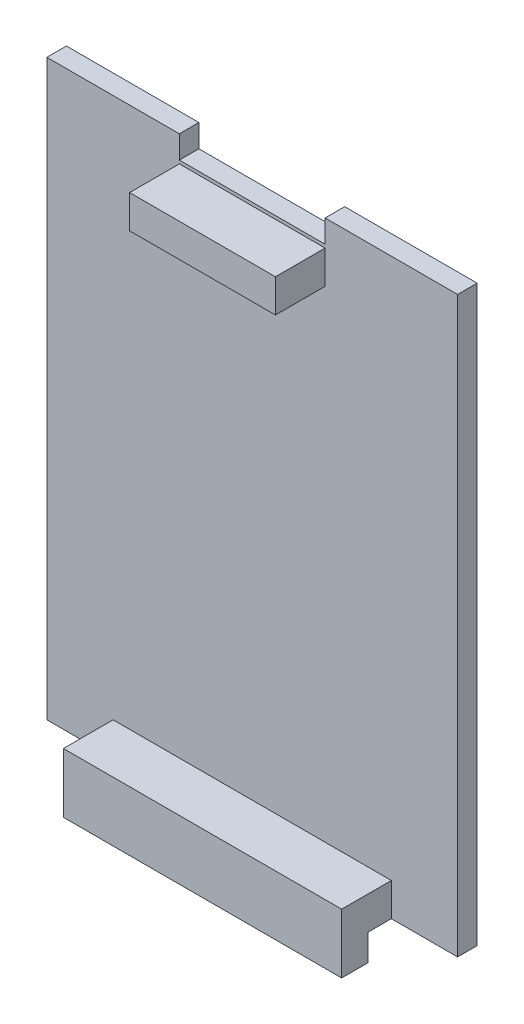
SolidWorks part; units mm, degrees
ref_plane "Front Plane" through (0, 0, 0) normal (0, 0, 1) x (1, 0, 0)
ref_plane "Top Plane" through (0, 0, 0) normal (0, 1, 0) x (1, 0, 0)
ref_plane "Right Plane" through (0, 0, 0) normal (1, 0, 0) x (0, 0, -1)
sketch "Sketch1" plane through (0, 0, 0) normal (0, 0, 1) x (1, 0, 0)
  line L1 (-2.7039, 44) -> (28.7961, 44)
  line L2 (-2.7039, 44) -> (-2.7039, 0)
  line L3 (-2.7039, 0) -> (28.7961, 0)
  line L4 (28.7961, 44) -> (28.7961, 0)
  dimension "D1" = 44
  dimension "D2" = 31.5
extrude "Boss-Extrude1" add sketch "Sketch1" along normal blind 1.5
sketch "Sketch2" plane through (0, 0, 1.5) normal (0, 0, 1) x (1, 0, 0)
  line L0 (28.7961, 44) -> (-2.7039, 44) construction
  line L1 (7.4561, 42) -> (18.6361, 42)
  line L2 (7.4561, 42) -> (7.4561, 39.46)
  line L3 (7.4561, 39.46) -> (18.6361, 39.46)
  line L4 (18.6361, 42) -> (18.6361, 39.46)
  line L5 (-2.7039, 44) -> (-2.7039, 0) construction
  line L6 (28.7961, 0) -> (28.7961, 44) construction
  dimension "D1" = 2
  dimension "D2" = 10.16
  dimension "D3" = 10.16
  dimension "D4" = 2.54
extrude "Boss-Extrude2" add sketch "Sketch2" along normal blind 3.81
sketch "Sketch4" plane through (0, 0, 1.5) normal (0, 0, 1) x (1, 0, 0)
  line L0 (28.7961, 44) -> (-2.7039, 44) construction
  line L1 (7.4561, 44) -> (18.6361, 44)
  line L2 (7.4561, 44) -> (7.4561, 42.254)
  line L3 (7.4561, 42.254) -> (18.6361, 42.254)
  line L4 (18.6361, 44) -> (18.6361, 42.254)
  line L5 (18.6361, 39.46) -> (18.6361, 42) construction
  line L6 (7.4561, 42) -> (7.4561, 39.46) construction
  line L7 (18.6361, 42) -> (7.4561, 42) construction
  point P4 (18.8865, 42.1398)
  point P5 (7.4419, 44)
  point P8 (0, 0)
  dimension "D1" = 0
  dimension "D2" = 0
  dimension "D3" = 0.254
extrude "Cut-Extrude1" cut sketch "Sketch4" against normal blind 3.81
sketch "Sketch5" plane through (0, 0, 1.5) normal (0, 0, 1) x (1, 0, 0)
  line L0 (-2.7039, 0) -> (28.7961, 0) construction
  line L1 (2.3761, 2.54) -> (23.7161, 2.54)
  line L2 (2.3761, 2.54) -> (2.3761, 0)
  line L3 (2.3761, 0) -> (23.7161, 0)
  line L4 (23.7161, 2.54) -> (23.7161, 0)
  line L5 (-2.7039, 44) -> (-2.7039, 0) construction
  line L6 (28.7961, 0) -> (28.7961, 44) construction
  point P6 (2.3761, 1.27)
  dimension "D1" = 0
  dimension "D2" = 2.54
  dimension "D3" = 5.08
  dimension "D4" = 5.08
extrude "Boss-Extrude3" add sketch "Sketch5" along normal blind 3.81
sketch "Sketch8" plane through (0, 0, 0) normal (0, -1, 0) x (-1, 0, 0)
  line L0 (-23.7161, -5.31) -> (-23.7161, -1.5) construction
  line L1 (-2.3761, -5.31) -> (-23.7161, -5.31)
  line L2 (-2.3761, -5.31) -> (-2.3761, -3.278)
  line L3 (-2.3761, -3.278) -> (-23.7161, -3.278)
  line L4 (-23.7161, -5.31) -> (-23.7161, -3.278)
  line L5 (-2.3761, -5.31) -> (-23.7161, -5.31) construction
  line L6 (-2.3761, -5.31) -> (-2.3761, -1.5) construction
  dimension "D1" = 2.032
  dimension "D2" = 0
  dimension "D3" = 0
extrude "Boss-Extrude4" add sketch "Sketch8" along normal blind 2.032
